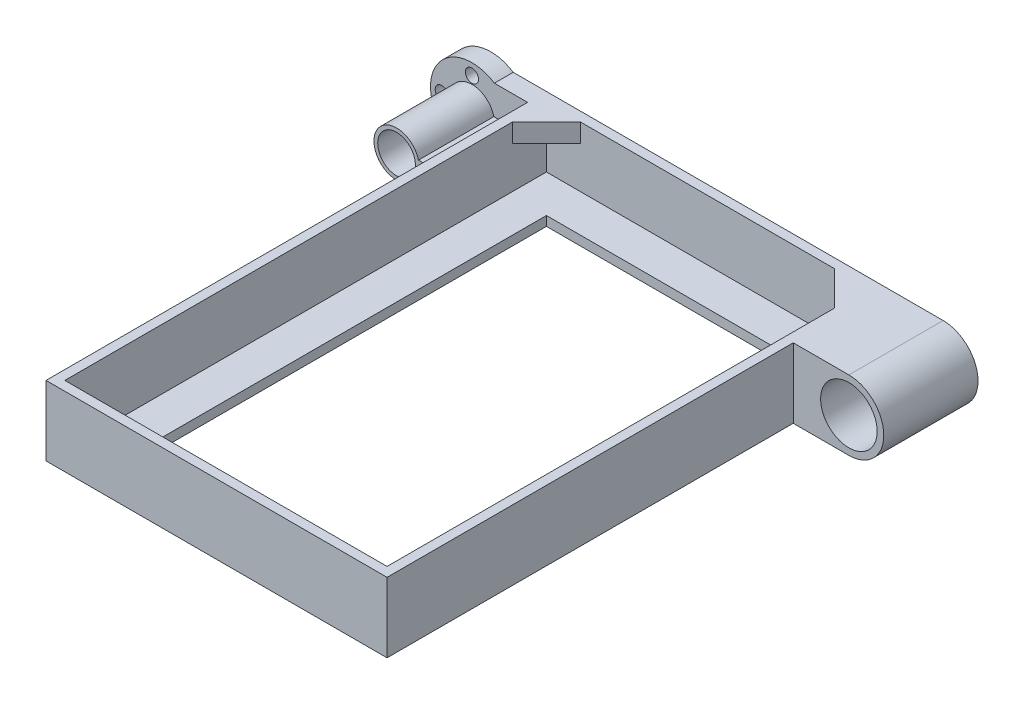
SolidWorks part; units mm, degrees
ref_plane "Front Plane" through (0, 0, 0) normal (0, 0, 1) x (1, 0, 0)
ref_plane "Top Plane" through (0, 0, 0) normal (0, 1, 0) x (1, 0, 0)
ref_plane "Right Plane" through (0, 0, 0) normal (1, 0, 0) x (0, 0, -1)
sketch "Sketch1" plane through (0, 0, 0) normal (0, 1, 0) x (1, 0, 0)
  line L0 (45.24, -66.38) -> (45.24, 66.38)
  line L1 (-42.74, -63.88) -> (42.74, -63.88)
  line L2 (-42.74, -63.88) -> (-42.74, 63.88)
  line L3 (-42.74, 63.88) -> (42.74, 63.88)
  line L4 (42.74, -63.88) -> (42.74, 63.88)
  line L5 (-42.74, -63.88) -> (42.74, 63.88) construction
  line L6 (-42.74, 63.88) -> (42.74, -63.88) construction
  line L7 (-45.24, 66.38) -> (45.24, 66.38)
  line L8 (-45.24, -66.38) -> (-45.24, 66.38)
  line L9 (-45.24, -66.38) -> (45.24, -66.38)
  point P0 (0, 0)
  dimension "D1" = 85.48
  dimension "D2" = 127.76
  dimension "D3" = 2.5
extrude "Boss-Extrude1" add sketch "Sketch1" along normal blind 16
sketch "Sketch2" plane through (0, 0, 0) normal (0, -1, 0) x (1, 0, 0)
  line L0 (45.24, -66.38) -> (-45.24, -66.38) construction
  line L1 (-45.24, -66.38) -> (-45.24, 66.38) construction
  line L2 (45.24, 66.38) -> (45.24, -66.38) construction
  line L3 (-45.24, 66.38) -> (45.24, 66.38) construction
  line L4 (45.24, -66.38) -> (-45.24, -66.38)
  line L5 (-45.24, -66.38) -> (-45.24, 66.38)
  line L6 (45.24, 66.38) -> (45.24, -66.38)
  line L7 (-45.24, 66.38) -> (45.24, 66.38)
extrude "Boss-Extrude2" add sketch "Sketch2" along normal blind 2.5
sketch "Sketch3" plane through (0, 0, -66.38) normal (0, 0, -1) x (-1, 0, 0)
  line L1 (-45.24, 16) -> (-60, 16)
  line L3 (-45.24, -2.5) -> (-60, -2.5)
  line L11 (0, -1000) -> (0, 49000) construction
  circle A0 centre (-60, 6.75) radius 7.5
  arc A3 (-60, 16) -> (-60, -2.5) centre (-60, 6.75) ccw
  line M17 (-45.24, 16) -> (-45.24, -2.5)
  dimension "D1" = 15
  dimension "D3" = 60
extrude "Boss-Extrude3" add sketch "Sketch3" against normal blind 25 contours L1 A3 L3 A0 M17
mirror "Mirror1" about plane through (0, 0, 0) normal (1, 0, 0) of "Boss-Extrude3"
sketch "Sketch4" plane through (0, 0, -66.38) normal (0, 0, -1) x (-1, 0, 0)
  circle A0 centre (60, 6.75) radius 5
  circle A1 centre (60, 6.75) radius 7.5 construction
  circle A2 centre (60, 6.75) radius 7.5
  dimension "D1" = 10
extrude "Boss-Extrude4" add sketch "Sketch4" against normal up to surface (25 mm away) up to face at (-52.5, 6.75, -41.38)
sketch "Sketch5" plane through (0, 0, -66.38) normal (0, 0, -1) x (-1, 0, 0)
  circle A0 centre (60, 6.75) radius 5 construction
  circle A1 centre (60, 6.75) radius 5
  circle A2 centre (60, 6.75) radius 11
  dimension "D1" = 22
extrude "Boss-Extrude5" add sketch "Sketch5" against normal blind 5
sketch "Sketch7" plane through (0, 0, -41.38) normal (0, 0, 1) x (1, 0, 0)
  line L3 (-45.24, -2.5) -> (-60, -2.5) construction
  line L4 (-45.24, 16) -> (-60, 16) construction
  line L5 (-45.24, -2.5) -> (-60, -2.5)
  line L6 (-45.24, 16) -> (-60, 16)
  line L7 (-45.24, 8.25) -> (-54.1905, 8.25)
  line L8 (-45.24, 16) -> (-45.24, -2.5) construction
  line L9 (-45.24, 5.25) -> (-54.1905, 5.25)
  line L11 (-45.24, 8.25) -> (-45.24, 16)
  line L12 (-45.24, 5.25) -> (-45.24, -2.5)
  arc A0 (-54.1905, 8.25) -> (-54.1905, 5.25) centre (-60, 6.75) ccw
  circle A1 centre (-60, 6.75) radius 5 construction
  circle A2 centre (-60, 6.75) radius 5
  arc A3 (-60, 16) -> (-60, -2.5) centre (-60, 6.75) ccw construction
  arc A4 (-60, 16) -> (-60, -2.5) centre (-60, 6.75) ccw
  dimension "D1" = 12
  dimension "D2" = 1.5
  dimension "D3" = 1.5
extrude "Cut-Extrude2" cut sketch "Sketch7" against normal up to surface (20 mm away) up to face at (-63.5743, 6.75, -61.38)
sketch "Sketch8" plane through (0, 0, -66.38) normal (0, 0, -1) x (-1, 0, 0)
  circle A0 centre (60, 6.75) radius 8 construction
  circle A1 centre (60, 14.75) radius 1.75
  circle A2 centre (68, 6.75) radius 1.75
  circle A3 centre (60, -1.25) radius 1.75
  dimension "D1" = 16
  dimension "D2" = 3.5
extrude "Cut-Extrude3" cut sketch "Sketch8" against normal up to next
sketch "Sketch9" plane through (0, 16, 0) normal (0, 1, 0) x (1, 0, 0)
  line L0 (33.74, 63.88) -> (42.74, 54.88)
  line L1 (42.74, 63.88) -> (-42.74, 63.88) construction
  line L2 (42.74, -63.88) -> (42.74, 63.88) construction
  line L3 (-42.74, 54.88) -> (-33.74, 63.88)
  line L4 (-42.74, 63.88) -> (-42.74, -63.88) construction
  line L5 (-33.74, 63.88) -> (-42.74, 63.88)
  line L6 (-42.74, 63.88) -> (-42.74, 54.88)
  line L7 (33.74, 63.88) -> (42.74, 63.88)
  line L8 (42.74, 63.88) -> (42.74, 54.88)
  dimension "D1" = 9
extrude "Boss-Extrude6" add sketch "Sketch9" against normal blind 5
sketch "Sketch10" plane through (0, 0, 0) normal (0, 1, 0) x (1, 0, 0)
  line L0 (32.74, 53.88) -> (-32.74, 53.88)
  line L1 (-32.74, 53.88) -> (-32.74, -53.88)
  line L2 (-32.74, -53.88) -> (32.74, -53.88)
  line L3 (32.74, -53.88) -> (32.74, 53.88)
  line L4 (-42.74, -63.88) -> (42.74, -63.88)
  line L5 (42.74, -63.88) -> (42.74, 63.88)
  line L6 (42.74, 63.88) -> (-42.74, 63.88)
  line L7 (-42.74, 63.88) -> (-42.74, -63.88)
  line L8 (-42.74, -63.88) -> (42.74, -63.88) construction
  line L9 (42.74, -63.88) -> (42.74, 63.88) construction
  line L10 (42.74, 63.88) -> (-42.74, 63.88) construction
  line L11 (-42.74, 63.88) -> (-42.74, -63.88) construction
  dimension "D1" = 0
  dimension "D2" = 10
extrude "Cut-Extrude4" cut sketch "Sketch10" against normal through all
